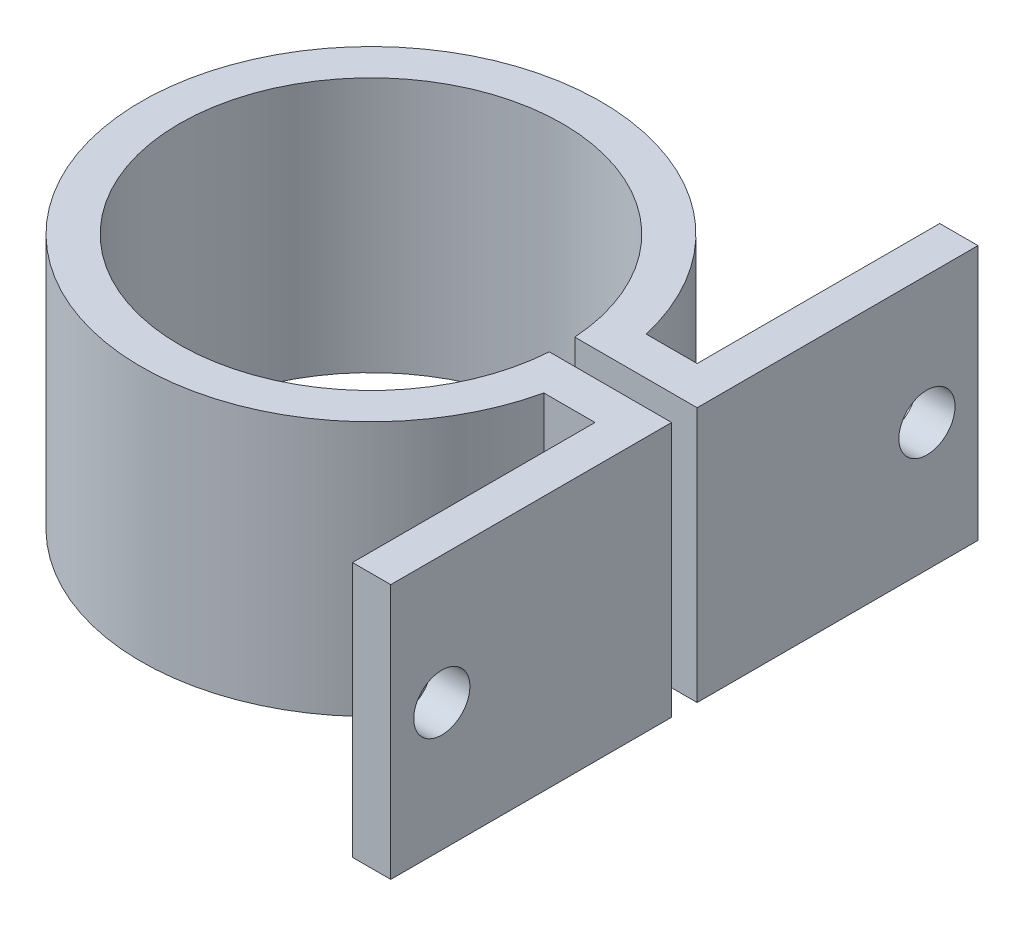
SolidWorks part; units mm, degrees
ref_plane "Front Plane" through (0, 0, 0) normal (0, 0, 1) x (1, 0, 0)
ref_plane "Top Plane" through (0, 0, 0) normal (0, 1, 0) x (1, 0, 0)
ref_plane "Right Plane" through (0, 0, 0) normal (1, 0, 0) x (0, 0, -1)
sketch "Sketch1" plane through (0, 0, 0) normal (0, 1, 0) x (1, 0, 0)
  line L0 (24.5499, -1) -> (24.5499, -5.6339)
  line L1 (17.5499, 4) -> (21.5499, 4)
  line L3 (17.5499, -4) -> (21.5499, -4)
  line L4 (24.5499, 9.7231) -> (24.5499, 1)
  line L5 (21.5499, 23) -> (24.5499, 23)
  line L6 (21.5499, 23) -> (21.5499, 4)
  line L7 (21.5499, -23) -> (24.5499, -23)
  line L8 (24.5499, 23) -> (24.5499, 1)
  line L9 (14.9666, 1) -> (24.5499, 1)
  line L11 (14.9666, -1) -> (24.5499, -1)
  line L13 (24.5499, -1) -> (24.5499, -23)
  line L14 (21.5499, -4) -> (21.5499, -23)
  line L15 (0, 18) -> (21.5499, 18) construction
  arc A0 (14.9666, 1) -> (14.9666, -1) centre (0, 0) ccw
  arc A1 (17.5499, 4) -> (17.5499, -4) centre (0, 0) ccw
  dimension "D2" = 3
  dimension "D5" = 15
  dimension "D1" = 3
  dimension "D3" = 3
  dimension "D4" = 2
  dimension "D6" = 4
  dimension "D7" = 5
extrude "Boss-Extrude1" add sketch "Sketch1" along normal blind 20 contours L1 A1 L3 L14 L7 L13 L0 L11 A0 L9 L4 L8 L5 L6
sketch "Sketch2" plane through (24.5499, 0, 0) normal (1, 0, 0) x (0, 0, -1)
  line L0 (-19, 20) -> (-19, 0) construction
  line L1 (-1, 20) -> (-23, 20) construction
  line L2 (-1, 0) -> (-23, 0) construction
  line L3 (-23, 20) -> (-23, 0) construction
  line L4 (23, 20) -> (23, 0) construction
  circle A0 centre (19, 10) radius 2.2
  circle A1 centre (-19, 10) radius 2.2
  point P10 (0, 0)
  point P11 (0, 0)
  point P12 (-16.6885, 10)
  dimension "D1" = 4.4
  dimension "D2" = 4
  dimension "D3" = 4
extrude "Cut-Extrude1" cut sketch "Sketch2" against normal up to surface (3 mm away) up to face at (21.5499, 10, 13.5)
